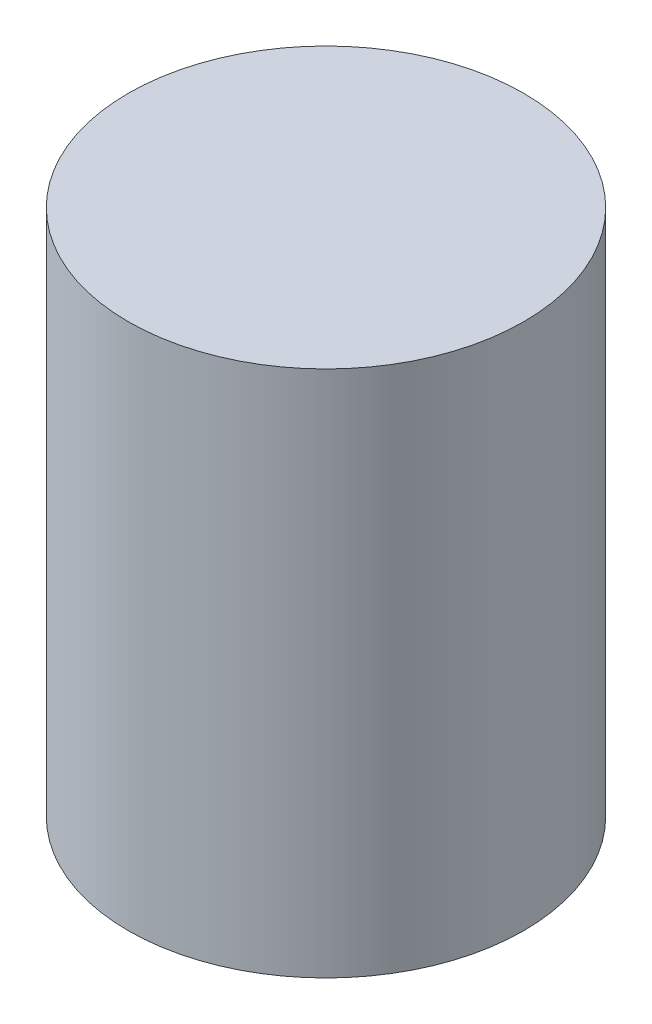
SolidWorks part; units mm, degrees
ref_plane "Front Plane" through (0, 0, 0) normal (0, 0, 1) x (1, 0, 0)
ref_plane "Top Plane" through (0, 0, 0) normal (0, 1, 0) x (1, 0, 0)
ref_plane "Right Plane" through (0, 0, 0) normal (1, 0, 0) x (0, 0, -1)
sketch "Sketch2" plane through (0, 0, 0) normal (0, 1, 0) x (1, 0, 0)
  circle A0 centre (0, 0) radius 2.3813
  dimension "D1" = 4.7625
extrude "Boss-Extrude1" add sketch "Sketch2" along normal blind 6.35
